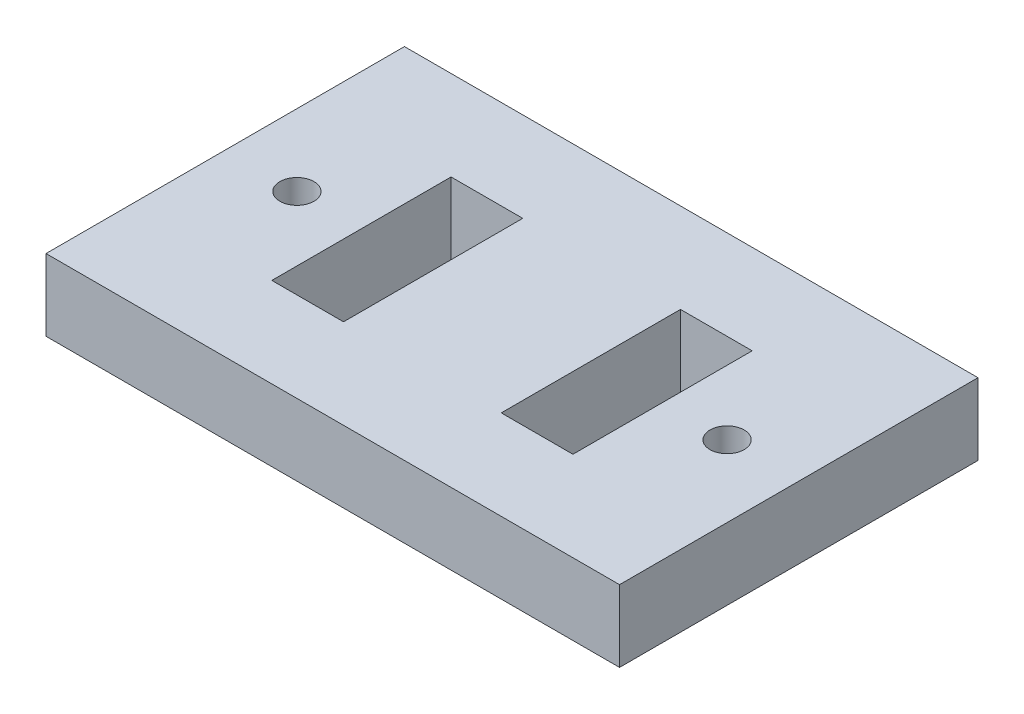
SolidWorks part; units mm, degrees
ref_plane "Front Plane" through (0, 0, 0) normal (0, 0, 1) x (1, 0, 0)
ref_plane "Top Plane" through (0, 0, 0) normal (0, 1, 0) x (1, 0, 0)
ref_plane "Right Plane" through (0, 0, 0) normal (1, 0, 0) x (0, 0, -1)
sketch "Sketch1" plane through (0, 0, 0) normal (0, 1, 0) x (1, 0, 0)
  line L1 (-40, -25) -> (40, -25)
  line L2 (-40, -25) -> (-40, 25)
  line L3 (-40, 25) -> (40, 25)
  line L4 (40, -25) -> (40, 25)
  line L5 (-40, -25) -> (40, 25) construction
  line L6 (-40, 25) -> (40, -25) construction
  point P0 (0, 0)
  dimension "D1" = 50
  dimension "D2" = 80
extrude "Boss-Extrude1" add sketch "Sketch1" along normal blind 10
sketch "Sketch2" plane through (0, 10, 0) normal (0, 1, 0) x (1, 0, 0)
  line L0 (40, -25) -> (40, 25) construction
  line L1 (-40, 25) -> (-40, -25) construction
  line L2 (40, 25) -> (-40, 25) construction
  circle A0 centre (-30, 0) radius 2.3813
  circle A1 centre (30, 0) radius 2.3812
  dimension "D1" = 4.7625
  dimension "D2" = 4.7625
  dimension "D3" = 10
  dimension "D4" = 10
  dimension "D5" = 25
  dimension "D6" = 25
extrude "Cut-Extrude1" cut sketch "Sketch2" against normal blind 10
sketch "Sketch3" plane through (0, 10, 0) normal (0, 1, 0) x (1, 0, 0)
  line L0 (-40, 25) -> (-40, -25) construction
  line L1 (-21, -12.5) -> (-11, -12.5)
  line L2 (-21, -12.5) -> (-21, 12.5)
  line L3 (-21, 12.5) -> (-11, 12.5)
  line L4 (-11, -12.5) -> (-11, 12.5)
  line L5 (-21, -12.5) -> (-11, 12.5) construction
  line L6 (-21, 12.5) -> (-11, -12.5) construction
  line L7 (11, -12.5) -> (21, -12.5)
  line L8 (11, -12.5) -> (11, 12.5)
  line L9 (11, 12.5) -> (21, 12.5)
  line L10 (21, -12.5) -> (21, 12.5)
  line L11 (11, -12.5) -> (21, 12.5) construction
  line L12 (11, 12.5) -> (21, -12.5) construction
  line L13 (40, -25) -> (40, 25) construction
  line L14 (40, 25) -> (-40, 25) construction
  point P0 (-16, 0)
  point P5 (16, 0)
  dimension "D1" = 25
  dimension "D2" = 25
  dimension "D3" = 0
  dimension "D4" = 0
  dimension "D5" = 10
  dimension "D6" = 10
  dimension "D7" = 16
  dimension "D8" = 16
  dimension "D9" = 19
  dimension "D10" = 19
  dimension "D11" = 22
  dimension "D12" = 12.5
extrude "Cut-Extrude2" cut sketch "Sketch3" against normal blind 10
